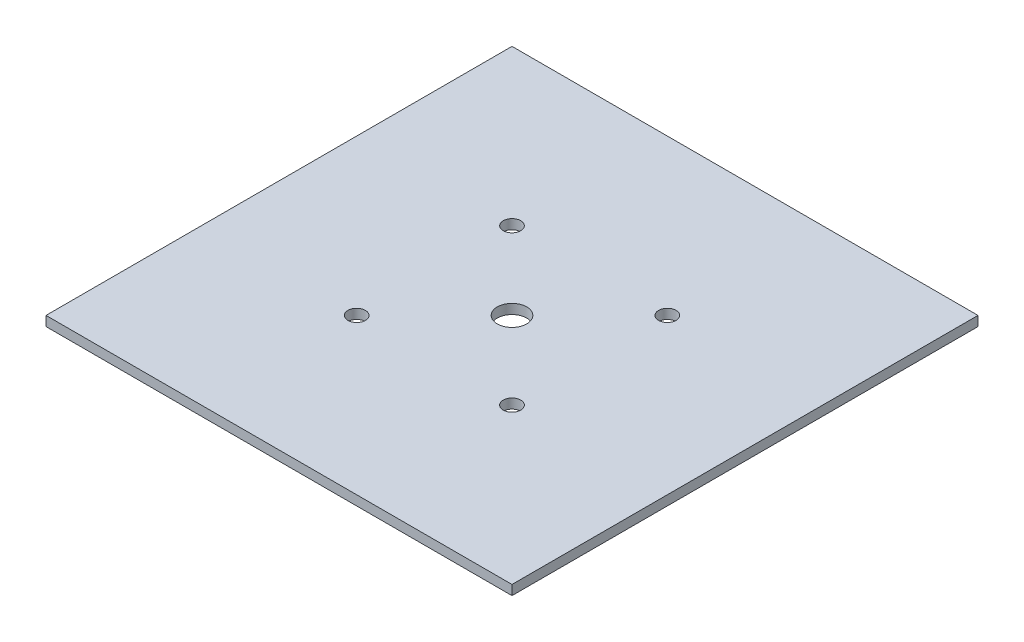
SolidWorks part; units mm, degrees
ref_plane "Front Plane" through (0, 0, 0) normal (0, 0, 1) x (1, 0, 0)
ref_plane "Top Plane" through (0, 0, 0) normal (0, 1, 0) x (1, 0, 0)
ref_plane "Right Plane" through (0, 0, 0) normal (1, 0, 0) x (0, 0, -1)
sketch "Sketch1" plane through (0, 0, 0) normal (0, 0, 1) x (1, 0, 0)
  line L10 (76.2, 1.5875) -> (-76.2, 1.5875)
  line L11 (76.2, 1.5875) -> (76.2, -1.5875)
  line L12 (76.2, -1.5875) -> (-76.2, -1.5875)
  line L13 (-76.2, 1.5875) -> (-76.2, -1.5875)
  line L14 (76.2, 1.5875) -> (-76.2, -1.5875) construction
  line L15 (76.2, -1.5875) -> (-76.2, 1.5875) construction
  point P0 (0, 0)
  dimension "D1" = 3.175
  dimension "D2" = 152.4
extrude "Boss-Extrude1" add sketch "Sketch1" along normal mid plane 152.4
sketch "Sketch2" plane through (0, 1.5875, 0) normal (0, 1, 0) x (1, 0, 0)
  line L1 (-22.5425, -25.4) -> (22.5425, -25.4)
  line L2 (-25.4, -22.5425) -> (-25.4, 22.5425)
  line L3 (-22.5425, 25.4) -> (22.5425, 25.4)
  line L4 (25.4, -22.5425) -> (25.4, 22.5425)
  line L5 (-23.3794, -23.3794) -> (23.3794, 23.3794) construction
  line L6 (-23.3794, 23.3794) -> (23.3794, -23.3794) construction
  circle A0 centre (-25.4, 25.4) radius 2.8575
  circle A1 centre (25.4, 25.4) radius 2.8575
  circle A2 centre (25.4, -25.4) radius 2.8575
  circle A3 centre (-25.4, -25.4) radius 2.8575
  circle A4 centre (0, 0) radius 4.826
  point P0 (0, 0)
  dimension "D2" = 5.715
  dimension "D3" = 9.652
  dimension "D1" = 50.8
extrude "Cut-Extrude1" cut sketch "Sketch2" against normal through all contours L2 A3 L1 | L3 A0 L2 | L1 A2 L4 | L4 A1 L3 | A4
